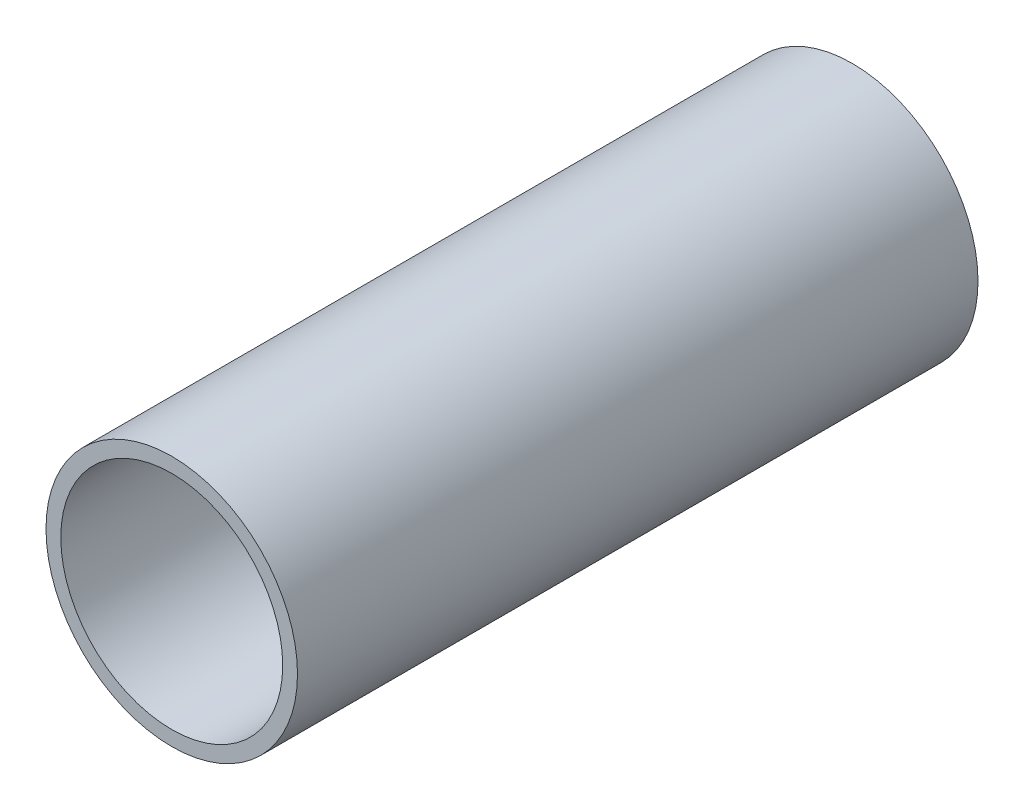
SolidWorks part; units mm, degrees
ref_plane "Front Plane" through (0, 0, 0) normal (0, 0, 1) x (1, 0, 0)
ref_plane "Top Plane" through (0, 0, 0) normal (0, 1, 0) x (1, 0, 0)
ref_plane "Right Plane" through (0, 0, 0) normal (1, 0, 0) x (0, 0, -1)
sketch "Sketch2" plane through (0, 0, 0) normal (0, 0, 1) x (1, 0, 0)
  circle A0 centre (0, 0) radius 85
  circle A1 centre (0, 0) radius 75
  dimension "D1" = 170
  dimension "D2" = 150
extrude "Boss-Extrude1" add sketch "Sketch2" along normal blind 460
